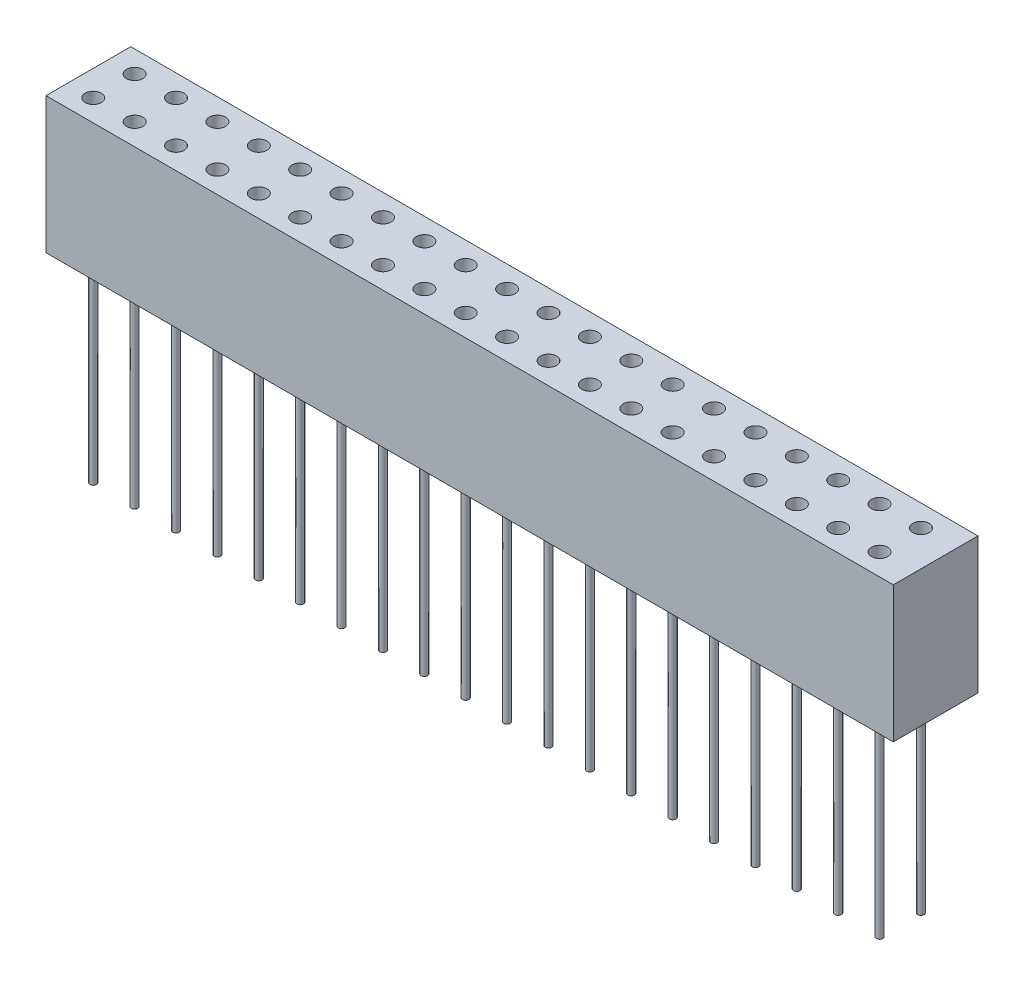
SolidWorks part; units mm, degrees
ref_plane "Front Plane" through (0, 0, 0) normal (0, 0, 1) x (1, 0, 0)
ref_plane "Top Plane" through (0, 0, 0) normal (0, 1, 0) x (1, 0, 0)
ref_plane "Right Plane" through (0, 0, 0) normal (1, 0, 0) x (0, 0, -1)
sketch "Sketch1" plane through (0, 0, 0) normal (0, 1, 0) x (1, 0, 0)
  line L1 (-26, -2.6) -> (26, -2.6)
  line L2 (-26, -2.6) -> (-26, 2.6)
  line L3 (-26, 2.6) -> (26, 2.6)
  line L4 (26, -2.6) -> (26, 2.6)
  line L5 (-26, -2.6) -> (26, 2.6) construction
  line L6 (-26, 2.6) -> (26, -2.6) construction
  point P0 (0, 0)
  dimension "D1" = 52
  dimension "D2" = 5.2
extrude "Boss-Extrude1" add sketch "Sketch1" along normal blind 8.35
sketch "Sketch2" plane through (0, 8.35, 0) normal (0, 1, 0) x (1, 0, 0)
  line L0 (-26, 2.6) -> (-26, -2.6) construction
  line L5 (-26, 1.27) -> (26, 1.27) construction
  line L6 (26, -2.6) -> (26, 2.6) construction
  line L7 (-26, -1.27) -> (26, -1.27) construction
  circle A0 centre (-24.43, 1.27) radius 0.5
  circle A1 centre (-24.43, -1.27) radius 0.5
  point P2 (-26, 0)
  dimension "D1" = 1
  dimension "D3" = 1
  dimension "D2" = 1.57
  dimension "D4" = 1.27
  dimension "D5" = 1.27
extrude "Cut-Extrude1" cut sketch "Sketch2" against normal blind 3
sketch "Sketch3" plane through (0, 0, 0) normal (0, -1, 0) x (1, 0, 0)
  line L0 (-26, -2.6) -> (-26, 2.6) construction
  line L4 (-26, 1.27) -> (26, 1.27) construction
  line L5 (26, 2.6) -> (26, -2.6) construction
  line L6 (-26, -1.27) -> (26, -1.27) construction
  circle A1 centre (-24.43, 1.27) radius 0.2
  circle A2 centre (-24.43, -1.27) radius 0.2
  point P5 (-26, 0)
  dimension "D2" = 1.57
  dimension "D4" = 1.27
  dimension "D1" = 0.4
  dimension "D3" = 1.27
extrude "Boss-Extrude2" add sketch "Sketch3" along normal blind 12.1
pattern_linear "LPattern1" count 20 spacing 2.54 along (1, 0, 0) of "Cut-Extrude1", "Boss-Extrude2"
equation "\"D3@Sketch2\"=\"D1@Sketch2\""
equation "\"D3@Sketch3\"=2.54/2"
equation "\"D4@Sketch3\"=\"D3@Sketch3\""
equation "\"D4@Sketch2\"=2.54/2"
equation "\"D5@Sketch2\"=\"D4@Sketch2\""
